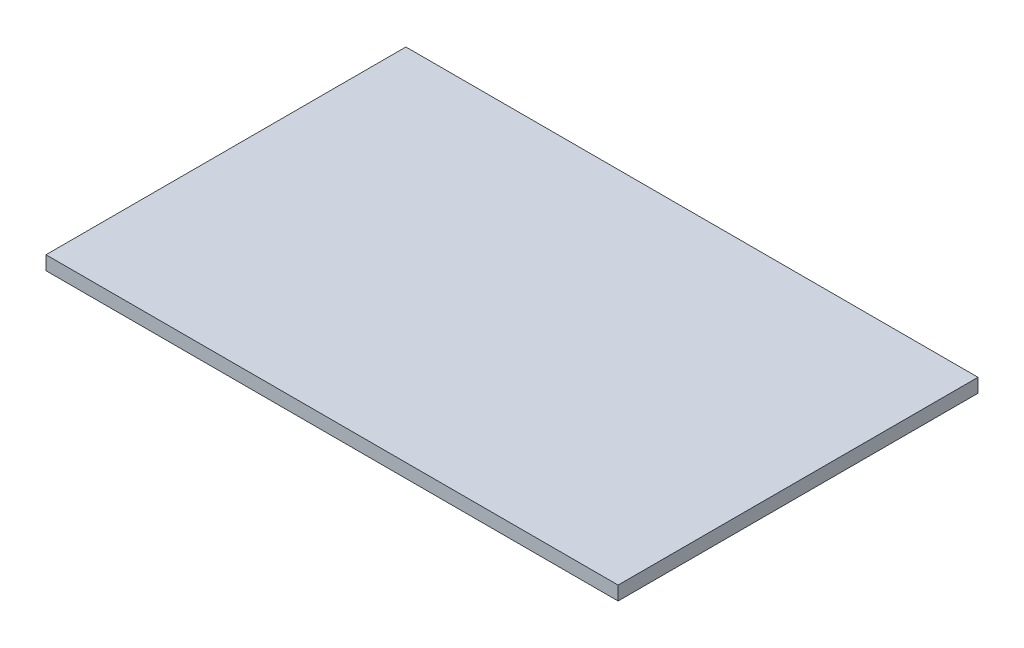
SolidWorks part; units mm, degrees
ref_plane "Front Plane" through (0, 0, 0) normal (0, 0, 1) x (1, 0, 0)
ref_plane "Top Plane" through (0, 0, 0) normal (0, 1, 0) x (1, 0, 0)
ref_plane "Right Plane" through (0, 0, 0) normal (1, 0, 0) x (0, 0, -1)
sketch "Sketch1" plane through (0, 0, 0) normal (0, 1, 0) x (1, 0, 0)
  line L1 (0, 0) -> (787.4, 0)
  line L2 (0, 0) -> (0, 495.3)
  line L3 (0, 495.3) -> (787.4, 495.3)
  line L4 (787.4, 0) -> (787.4, 495.3)
  dimension "D1" = 787.4
  dimension "D2" = 495.3
extrude "Boss-Extrude1" add sketch "Sketch1" along normal blind 19.05
